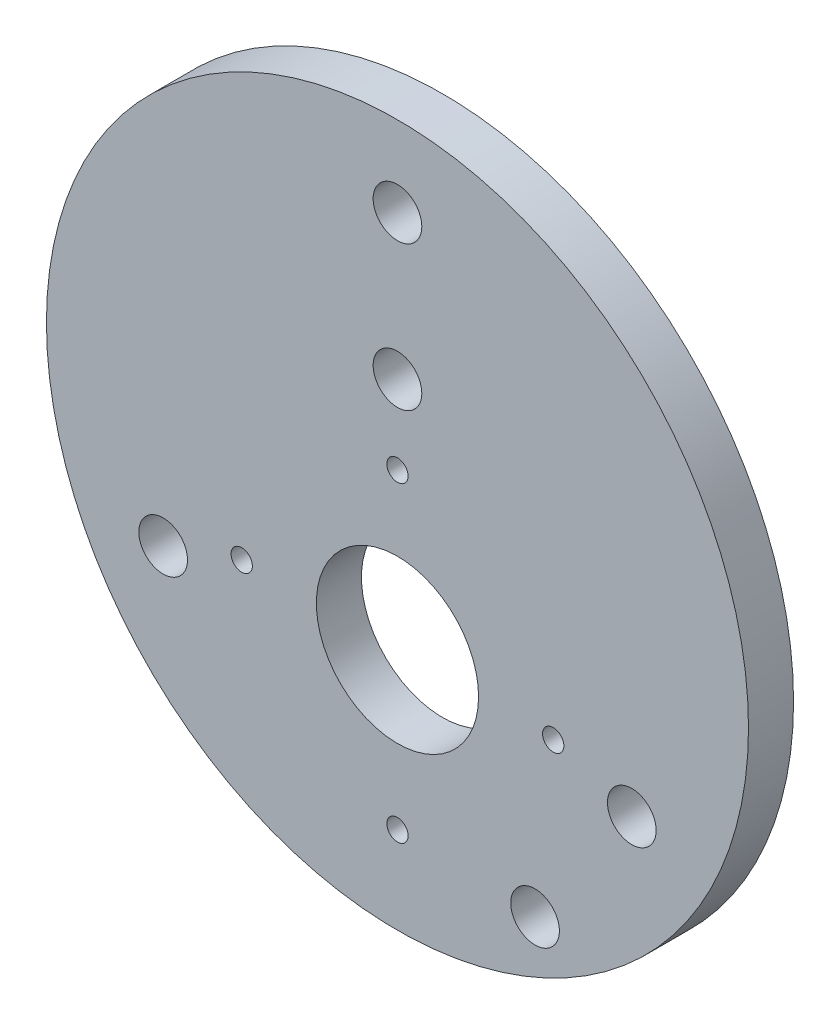
SolidWorks part; units mm, degrees
ref_plane "Front Plane" through (0, 0, 0) normal (0, 0, 1) x (1, 0, 0)
ref_plane "Top Plane" through (0, 0, 0) normal (0, 1, 0) x (1, 0, 0)
ref_plane "Right Plane" through (0, 0, 0) normal (1, 0, 0) x (0, 0, -1)
sketch "Sketch1" plane through (0, 0, 0) normal (0, 0, 1) x (1, 0, 0)
  circle A0 centre (0, 0) radius 49.4665
  dimension "D1" = 98.933
extrude "Boss-Extrude1" add sketch "Sketch1" along normal blind 6.35
sketch "Sketch2" plane through (0, 0, 6.35) normal (0, 0, 1) x (1, 0, 0)
  line L0 (0, -37.1877) -> (0, 6.7077) construction
  line L1 (-21.9477, -15.24) -> (0, 6.7077)
  line L2 (-21.9477, -15.24) -> (0, -37.1877)
  line L3 (0, -37.1877) -> (21.9477, -15.24)
  line L4 (0, 6.7077) -> (21.9477, -15.24)
  line L5 (0, -15.24) -> (12.0918, -15.24) construction
  point P4 (0, -15.24)
  dimension "D1" = 31.0388
  dimension "D2" = 31.0388
  dimension "D3" = 15.24
  dimension "D4" = 90
hole_wizard "M3 Screw Hole - Ø3.0mm Dowel Hole" positions "Sketch3" profile "Sketch4" hole size "Ø3.0" standard "ANSI Metric" end condition through all
sketch "Sketch3" plane through (0, 0, 6.35) normal (0, 0, 1) x (1, 0, 0)
  point P0 (0, 6.7077)
  point P3 (-21.9477, -15.24)
  point P6 (0, -37.1877)
  point P9 (21.9477, -15.24)
sketch "Sketch4" plane through (0, 6.7077, 6.35) normal (1, 0, 0) x (0, -1, 0)
  line L0 (0, 0) -> (0, 6.35)
  line L1 (0, 6.35) -> (1.5, 6.35)
  line L2 (1.5, 6.35) -> (1.5, 0)
  line L5 (1.5, 0) -> (0, 0)
  line L11 (0, -6.35) -> (0, 107.95) construction
  dimension "Thru Hole Dia." = 3
  dimension "Thru Hole Depth" = 6.35
sketch "Sketch5" plane through (0, 0, 6.35) normal (0, 0, 1) x (1, 0, 0)
  line L0 (0, -37.1877) -> (0, 6.7077) construction
  line L1 (-29.9941, -15.24) -> (0, 14.7541) construction
  line L2 (-29.9941, -15.24) -> (0, -45.2341) construction
  line L3 (0, -45.2341) -> (29.9941, -15.24) construction
  line L4 (0, 14.7541) -> (29.9941, -15.24) construction
  line L5 (-29.9941, -15.24) -> (29.9941, -15.24) construction
  line L6 (0, -45.2341) -> (0, 14.7541) construction
  line L7 (-19.3974, 4.1574) -> (0, -15.24) construction
  line L8 (0, -15.24) -> (19.3974, -15.24) construction
  line L9 (0, -15.24) -> (19.3974, -34.6374) construction
  line L10 (0, -15.24) -> (-3.0533, -18.2933) construction
  line L11 (-3.0533, -18.2933) -> (16.3441, -37.6906) construction
  line L12 (0, -15.24) -> (-19.3974, -34.6374) construction
  line L13 (0, -15.24) -> (-18.3197, 3.0797) construction
  circle A0 centre (0, 17.78) radius 3.429
  circle A1 centre (16.3441, -37.6906) radius 3.429
  circle A2 centre (-19.3974, -34.6374) radius 3.429
  point P0 (0, -15.24)
  point P7 (0, -15.24)
  point P21 (0, 0)
  point P22 (0, 0)
  point P23 (0, 0)
  point P24 (0, 0)
  point P25 (0, 0)
  point P26 (0, 0)
  point P28 (0, 0)
  point P29 (0, 0)
  dimension "D3" = 27.432
  dimension "D5" = 27.432
  dimension "D9" = 6.858
  dimension "D1" = 17.78
  dimension "D2" = 4.318
  dimension "D4" = 42.418
  dimension "D6" = 27.432
  dimension "D7" = 135
  dimension "D8" = 25.908
sketch "Sketch6" plane through (0, 0, 6.35) normal (0, 0, 1) x (1, 0, 0)
  line L0 (0, 38.1282) -> (-33.02, -19.0641) construction
  line L1 (-33.02, -19.0641) -> (33.02, -19.0641) construction
  line L2 (33.02, -19.0641) -> (0, 38.1282) construction
  line L3 (-33.02, -19.0641) -> (0, 0) construction
  line L4 (0, 0) -> (33.02, -19.0641) construction
  line L5 (0, 0) -> (0, 38.1282) construction
  circle A0 centre (0, 38.1282) radius 3.429
  circle A1 centre (-33.02, -19.0641) radius 3.429
  circle A2 centre (33.02, -19.0641) radius 3.429
  dimension "D1" = 6.858
  dimension "D2" = 66.04
  dimension "D3" = 60
  dimension "D4" = 60
extrude "Cut-Extrude2" cut sketch "Sketch6" against normal through all
sketch "Sketch7" plane through (0, 0, 6.35) normal (0, 0, 1) x (1, 0, 0)
  line L0 (0, -37.1877) -> (0, 6.7077) construction
  circle A0 centre (0, -15.24) radius 11.43
  point P4 (0, -15.24)
  dimension "D1" = 22.86
extrude "Cut-Extrude3" cut sketch "Sketch7" against normal through all
sketch "Possible Plate Hole Reference" plane through (0, 0, 6.35) normal (0, 0, 1) x (1, 0, 0)
  line L0 (47.781, 12.8029) -> (-47.781, -12.8029) construction
  line L1 (0, 0) -> (49.4665, 0) construction
  circle A0 centre (0, 0) radius 49.4665 construction
  circle A1 centre (0, 0) radius 4.9466 construction
  circle A2 centre (0, 0) radius 49.4665 construction
  point P7 (0, 0)
  dimension "D2" = 9.8933
  dimension "D3" = 98.933
  dimension "D1" = 15
extrude "Cut-Extrude4" cut sketch "Sketch5" against normal through all contours A0
sketch "Sketch11" plane through (0, 0, 6.35) normal (0, 0, 1) x (1, 0, 0)
  line L0 (0, 17.78) -> (0, -59.7695) construction
  line L4 (0, 17.78) -> (19.3897, -38.1355) construction
  line L5 (19.3897, -38.1355) -> (0, -38.1355) construction
  circle A0 centre (19.3897, -38.1355) radius 3.429
  circle A3 centre (0, 17.78) radius 3.429 construction
  dimension "D1" = 19.125
  dimension "D2" = 6.858
  dimension "D6" = 59.182
extrude "Cut-Extrude7" cut sketch "Sketch11" against normal through all
equation "\"D2@Possible Plate Hole Reference\" = 0.1 * \"D3@Possible Plate Hole Reference\""
